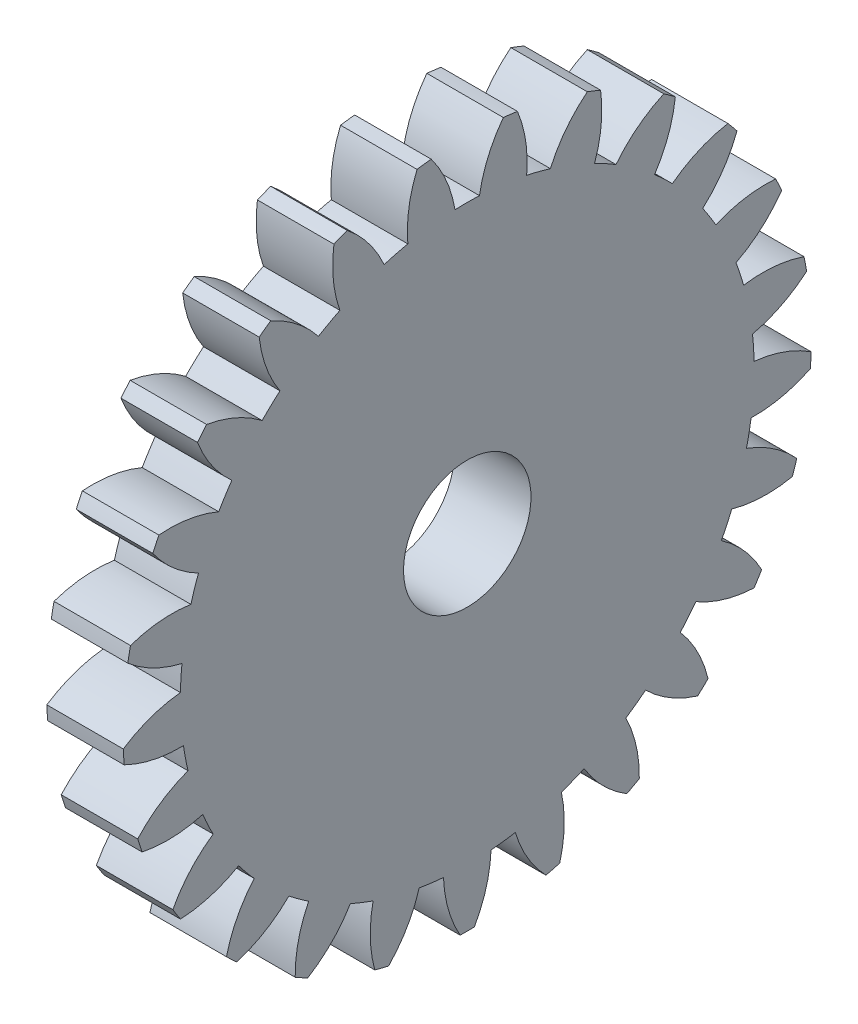
SolidWorks part; units mm, degrees
ref_plane "Plane1" through (0, 0, 0) normal (0, 0, 1) x (1, 0, 0)
ref_plane "Plane2" through (0, 0, 0) normal (0, 1, 0) x (1, 0, 0)
ref_plane "Plane3" through (0, 0, 0) normal (1, 0, 0) x (0, 0, -1)
sketch "HoldingSke" plane through (0, 0, 0) normal (0, 1, 0) x (1, 0, 0)
  line L0 (0, 0) -> (0.9063, -0.4226)
  line L1 (-15, 0) -> (100, 0) construction
  line L2 (0, 0) -> (-2.1039, 2.3779)
  line L3 (0, 0) -> (-11.863, 4.5341)
  line L4 (0, 0) -> (7.8269, 3.6497)
  line L5 (0, 0) -> (-46.8476, -17.4728)
  line L6 (0, 0) -> (-2.4869, -1.6779)
  line L7 (-2.1039, 2.3779) -> (8.6586, 51.2059)
  line L8 (-76.2, 54.61) -> (-75.3, 54.61)
  line L9 (-71.009, 38.7566) -> (-53.1078, 45.2721)
  line L10 (-76.2, 71.12) -> (104.1128, 71.12)
  line L11 (0, 0) -> (-3, 0)
  line L12 (-76.2, 101.6) -> (-76.162, 101.6)
  line L13 (24.9733, 27.94) -> (52.9518, 28.4284)
  line L14 (24.9733, 27.94) -> (24.9743, 27.94)
  line L15 (24.9733, 27.94) -> (100.4006, 29.5858)
  line L16 (-63.627, -1) -> (-12.827, -1)
  circle A0 centre (0, 0) radius 2.5
  circle A1 centre (0, 0) radius 11.249
  circle A2 centre (0, 0) radius 37.5
  circle A3 centre (0, 0) radius 2.5
  dimension "MHD" = 22.498
  dimension "Hub_dia" = 75
  dimension "Bore" = 5
  dimension "MBD" = 5
  dimension "Num_teeth" = 25
  dimension "Pitch_radius" = 180.3128
  dimension "Pitch" = 1
  dimension "Width" = 3
  dimension "Overall_len" = 50
  dimension "Show_teeth" = 25
  dimension "Thickness" = 3
  dimension "OAL" = 50.0001
  dimension "T_dim" = 0.9
  dimension "Ap" = 20
  dimension "H" = 19.05
  dimension "Backlash" = 0.038
  dimension "Addendum_fac" = 1
  dimension "Dedendum_fac" = 1.25
  dimension "Clearance_fac" = 0.25
  dimension "Dedendum_add" = 0.001
  dimension "Module" = 1
sketch "BasProSke" plane through (0, 0, 0) normal (0, 1, 0) x (1, 0, 0)
  line L0 (-10, 0) -> (60, 0) construction
  line L1 (0, 0) -> (0, 13.5)
  line L2 (0, 0) -> (3, 0)
  line L3 (3, 0) -> (3, 13.5)
  line L4 (3, 13.5) -> (0, 13.5)
  dimension "Diameter" = 27
  dimension "Thickness" = 3
revolve "Base-Revolve" add sketch "BasProSke" angle 360 about L0
sketch "TooCutSke" plane through (0, 0, 0) normal (1, 0, 0) x (0, 0, -1)
  line L1 (0, 0) -> (0, 107) construction
  line L2 (0, 0) -> (-0.8514, 12.471) construction
  line L3 (0, 0) -> (-3.1282, 24.7619) construction
  line L4 (-0.8514, 12.471) -> (-1.5641, 12.3809) construction
  arc A0 (0.4801, 11.2388) -> (-0.4801, 11.2388) centre (0, 0) ccw
  arc A1 (1.4322, 13.4494) -> (-1.4322, 13.4494) centre (0, 0) ccw
  circle A2 centre (0, 0) radius 12.5 construction
  circle A3 centre (0, 0) radius 11.7462 construction
  arc A4 (-0.4801, 11.2388) -> (-1.4322, 13.4494) centre (-5.4133, 10.4244) ccw
  arc A5 (1.4322, 13.4494) -> (0.4801, 11.2388) centre (5.4133, 10.4244) ccw
  dimension "Root_dia" = 22.498
  dimension "Overcut_dia" = 27.0508
  dimension "Pitch_dia" = 25
  dimension "Base_dia" = 23.4923
  dimension "Flank_rad" = 5
  dimension "Half_ang" = 7.2
  dimension "Half_CT" = 0.7184
extrude "ToothCut" cut sketch "TooCutSke" along normal through all
fillet "Breaks" [suppressed] radius 0.02
fillet "RootFillets" [suppressed] radius 0.251
pattern_circular "TeethCuts" count 25 every 14.4 about axis through (-10, 0, 0) along (1, 0, 0) of "ToothCut", "RootFillets", "Breaks"
sketch "HubNeaOneSke" plane through (0, 0, 0) normal (-1, 0, 0) x (0, 0, 1)
  circle A0 centre (0, 0) radius 11.249
  dimension "Diameter" = 22.498
extrude "HubNearOne" [suppressed] add sketch "HubNeaOneSke" along normal blind 47.0001
sketch "HubNeaBotSke" plane through (0, 0, 0) normal (-1, 0, 0) x (0, 0, 1)
  circle A0 centre (0, 0) radius 11.249
  dimension "Diameter" = 22.498
extrude "HubNearBoth" [suppressed] add sketch "HubNeaBotSke" along normal blind 23.5
ref_plane "FarPln" through (3, 0, 0) normal (1, 0, 0) x (0, 0, -1)
sketch "HubFarSke" plane through (3, 0, 0) normal (1, 0, 0) x (0, 0, -1)
  circle A0 centre (0, 0) radius 11.249
  dimension "Diameter" = 22.498
extrude "HubFar" [suppressed] add sketch "HubFarSke" along normal blind 23.5
sketch "BorSke" plane through (0, 0, 0) normal (1, 0, 0) x (0, 0, -1)
  circle A0 centre (0, 0) radius 2.5
  dimension "Diameter" = 5
extrude "Bore" cut sketch "BorSke" along normal mid plane 100.0001
sketch "KeySke" plane through (0, 0, 0) normal (1, 0, 0) x (0, 0, -1)
  line L0 (-1, 0) -> (-1, 3.4)
  line L1 (-1, 3.4) -> (1, 3.4)
  line L2 (1, 3.4) -> (1, 0)
  line L3 (0, 0) -> (0, 34) construction
  line L4 (-1, 0) -> (1, 0)
  dimension "Offset" = 3.4
  dimension "Width" = 2
extrude "Keyway" [suppressed] cut sketch "KeySke" along normal mid plane 100.0001
pattern_circular "Keyway2" [suppressed] count 2 every 90 about axis through (-10, 0, 0) along (1, 0, 0)
equation "' \"Module@HoldingSke\" = 6.35"
equation "' \"Num_teeth@HoldingSke\" = 12"
equation "' \"Ap@HoldingSke\" =  20"
equation "' \"Width@HoldingSke\" = 0.5 * 25.4"
equation "' \"Hub_dia@HoldingSke\"= 1 * 25.4"
equation "' \"Overall_len@HoldingSke\" = 1.0 * 25.4"
equation "' \"Bore@HoldingSke\" = 0.75 * 25.4"
equation "' \"T_dim@HoldingSke\" = 0.1 * 25.4"
equation "' \"Width@KeySke\" = 0.25 * 25.4"
equation "' \"Show_teeth@HoldingSke\" = 13"
equation "' \"Backlash@HoldingSke\" = 0.009 * 25.4"
equation "' \"Addendum_fac@HoldingSke\" = 1.0"
equation "' \"Dedendum_fac@HoldingSke\" = 1.25"
equation "' \"Dedendum_add@HoldingSke\" = 0.00005 * 25.4"
equation "' \"Clearance_fac@HoldingSke\" = 0.25"
equation "\"Pitch@HoldingSke\" = 1 / \"Module@HoldingSke\""
equation "\"Overcut_dia@TooCutSke\" = (\"Num_teeth@HoldingSke\" + 2 * \"Addendum_fac@HoldingSke\") / \"Pitch@HoldingSke\" + 0.002 * 25.4"
equation "\"Pitch_dia@TooCutSke\" = \"Num_teeth@HoldingSke\" / \"Pitch@HoldingSke\""
equation "\"Base_dia@TooCutSke\" = \"Num_teeth@HoldingSke\" / \"Pitch@HoldingSke\" * cos((\"Ap@HoldingSke\"  * 3.14159265 / 180))"
equation "\"Root_dia@TooCutSke\" = (\"Num_teeth@HoldingSke\" + 2) / \"Pitch@HoldingSke\" - 2 * (\"Addendum_fac@HoldingSke\" + \"Dedendum_fac@HoldingSke\") / \"Pitch@HoldingSke\" - \"Dedendum_add@HoldingSke\" * 2"
equation "\"Half_ang@TooCutSke\" = 180 / \"Num_teeth@HoldingSke\""
equation "\"Half_CT@TooCutSke\" = \"Num_teeth@HoldingSke\" / \"Pitch@HoldingSke\" * sin((3.14159265 / 2 / \"Num_teeth@HoldingSke\")) / 2 - 7 * \"Backlash@HoldingSke\" / 4"
equation "\"Flank_rad@TooCutSke\" = \"Num_teeth@HoldingSke\" / \"Pitch@HoldingSke\" / 5"
equation "\"Radius@RootFillets\" = \"Clearance_fac@HoldingSke\" / \"Pitch@HoldingSke\" + \"Dedendum_add@HoldingSke\""
equation "\"Break_rad@Breaks\" = 0.02 / \"Pitch@HoldingSke\""
equation "\"Thickness@HoldingSke\" = \"Width@HoldingSke\""
equation "\"OAL@HoldingSke\" = \"Thickness@HoldingSke\""
equation "\"MHD@HoldingSke\" = (\"Num_teeth@HoldingSke\" + 2) / \"Pitch@HoldingSke\" - 2 * (\"Addendum_fac@HoldingSke\" + \"Dedendum_fac@HoldingSke\")  / \"Pitch@HoldingSke\" - \"Dedendum_add@HoldingSke\" * 2"
equation "\"MBD@HoldingSke\" = (\"Num_teeth@HoldingSke\" + 2) / \"Pitch@HoldingSke\" - 2 * (\"Addendum_fac@HoldingSke\" + \"Dedendum_fac@HoldingSke\")  / \"Pitch@HoldingSke\" - \"Dedendum_add@HoldingSke\" * 2 - 0.002 * 25.4"
equation "\"MHD@HoldingSke\" = ((sgn( \"MHD@HoldingSke\" - \"Hub_dia@HoldingSke\" )-1)*( \"MHD@HoldingSke\" - \"Hub_dia@HoldingSke\" ))/-2+ \"Hub_dia@HoldingSke\""
equation "\"MBD@HoldingSke\" = ((sgn( \"MBD@HoldingSke\" - \"Bore@HoldingSke\" )-1)*( \"MBD@HoldingSke\" - \"Bore@HoldingSke\" ))/-2+ \"Bore@HoldingSke\""
equation "\"OAL@HoldingSke\" = ((sgn( \"OAL@HoldingSke\" - \"Overall_len@HoldingSke\" )+1)*( \"OAL@HoldingSke\" - \"Overall_len@HoldingSke\" ))/2 + \"Overall_len@HoldingSke\" + 0.000002 * 25.4"
equation "\"Num_teeth@TeethCuts\" = int( \"Show_teeth@HoldingSke\" ) + 1"
equation "\"Num_teeth@TeethCuts\" = ((sgn( \"Num_teeth@TeethCuts\" - \"Num_teeth@HoldingSke\" )-1)*( \"Num_teeth@TeethCuts\" - \"Num_teeth@HoldingSke\" ))/-2+ \"Num_teeth@HoldingSke\""
equation "\"Num_teeth@TeethCuts\" = ((sgn( \"Num_teeth@TeethCuts\" - 2.0)+1)*( \"Num_teeth@TeethCuts\" - 2.0))/2 +2.0"
equation "\"Angle@TeethCuts\" = 360.0 / \"Num_teeth@HoldingSke\""
equation "\"Diameter@BasProSke\" = (\"Num_teeth@HoldingSke\" + 2 * \"Addendum_fac@HoldingSke\") / \"Pitch@HoldingSke\""
equation "\"Thickness@BasProSke\"  = \"Thickness@HoldingSke\""
equation "' \"Fillet_rad@BasProSke\" =  \"Thickness@HoldingSke\" * 0.05"
equation "\"MHD@HoldingSke\" = ((sgn( \"MHD@HoldingSke\" - \"Root_dia@TooCutSke\" )-1)*( \"MHD@HoldingSke\" - \"Root_dia@TooCutSke\" ))/-2+ \"Root_dia@TooCutSke\""
equation "\"Diameter@HubNeaOneSke\" = \"MHD@HoldingSke\""
equation "\"Length@HubNearOne\" = \"OAL@HoldingSke\" - \"Thickness@BasProSke\""
equation "\"Diameter@HubNeaBotSke\" = \"MHD@HoldingSke\""
equation "\"Length@HubNearBoth\" = ( \"OAL@HoldingSke\" - \"Thickness@BasProSke\" ) / 2.0"
equation "\"Thickness@FarPln\" = \"Thickness@BasProSke\""
equation "\"Diameter@HubFarSke\" = \"MHD@HoldingSke\""
equation "\"Length@HubFar\" = ( \"OAL@HoldingSke\" - \"Thickness@BasProSke\" ) / 2.0"
equation "\"Diameter@BorSke\" = \"MBD@HoldingSke\""
equation "\"D1@Bore\" = \"OAL@HoldingSke\" * 2.0"
equation "\"D1@Keyway\" = \"OAL@HoldingSke\" * 2.0"
equation "\"Offset@KeySke\" = \"T_dim@HoldingSke\" + \"MBD@HoldingSke\" / 2.0"
